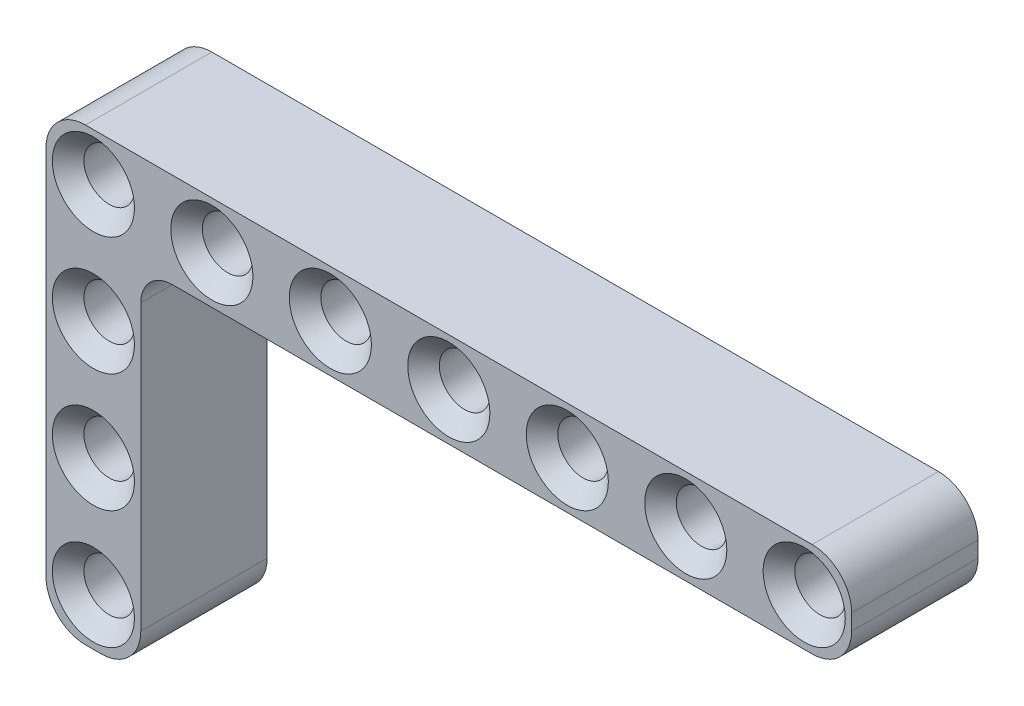
SolidWorks part; units mm, degrees
ref_plane "Front Plane" through (0, 0, 0) normal (0, 0, 1) x (1, 0, 0)
ref_plane "Top Plane" through (0, 0, 0) normal (0, 1, 0) x (1, 0, 0)
ref_plane "Right Plane" through (0, 0, 0) normal (1, 0, 0) x (0, 0, -1)
sketch "Sketch1" plane through (0, 0, 0) normal (0, 0, 1) x (1, 0, 0)
  line L1 (-0.5, 3) -> (45.5, 3)
  line L2 (-3, 0.5) -> (-3, -0.5)
  line L3 (-0.5, -3) -> (45.5, -3)
  line L4 (48, 0.5) -> (48, -0.5)
  circle A0 centre (0, 0) radius 1.6
  arc A1 (45.5, -3) -> (48, -0.5) centre (45.5, -0.5) ccw
  arc A2 (45.5, 3) -> (48, 0.5) centre (45.5, 0.5) cw
  arc A3 (-3, -0.5) -> (-0.5, -3) centre (-0.5, -0.5) ccw
  arc A4 (-0.5, 3) -> (-3, 0.5) centre (-0.5, 0.5) ccw
  circle A5 centre (7.5, 0) radius 1.6
  circle A6 centre (15, 0) radius 1.6
  circle A7 centre (22.5, 0) radius 1.6
  circle A8 centre (30, 0) radius 1.6
  circle A9 centre (37.5, 0) radius 1.6
  circle A10 centre (45, 0) radius 1.6
  point P8 (-3, 0)
  point P14 (-3, -3)
  point P17 (-3, 3)
  dimension "D1" = 3.2
  dimension "D4" = 2.5
  dimension "D2" = 6
  dimension "D3" = 3
  dimension "D6" = 7.5
  dimension "D5" = 7
extrude "Boss-Extrude1" add sketch "Sketch1" along normal blind 8
chamfer "Chamfer1" distance 1 angle 45 10 edges at (31.6, 0, 0) (31.6, 0, 8) (24.1, 0, 0) (24.1, 0, 8) (16.6, 0, 0) (16.6, 0, 8) (9.1, 0, 0) (9.1, 0, 8) (1.6, 0, 0) (1.6, 0, 8)
sketch "Sketch2" plane through (0, 0, 8) normal (0, 0, 1) x (1, 0, 0)
  line L0 (-3, 0) -> (-3, -23)
  line L1 (-0.5, -25.5) -> (0.5, -25.5)
  line L2 (3, -23) -> (3, -3)
  line L3 (-3, 0.5) -> (-3, -0.5) construction
  line L4 (-0.5, -3) -> (45.5, -3) construction
  circle A1 centre (0, -7.5) radius 1.6
  arc A4 (-3, -23) -> (-0.5, -25.5) centre (-0.5, -23) ccw
  arc A5 (0.5, -25.5) -> (3, -23) centre (0.5, -23) ccw
  circle A6 centre (0, -15) radius 1.6
  circle A7 centre (0, -22.5) radius 1.6
  point P18 (-3, -25.5)
  point P21 (3, -25.5)
  dimension "D3" = 3.2
  dimension "D8" = 2.5
  dimension "D1" = 6
  dimension "D2" = 90
  dimension "D4" = 3
  dimension "D5" = 7.5
  dimension "D7" = 3
  dimension "D6" = 3
extrude "Boss-Extrude3" add sketch "Sketch2" against normal blind 8
fillet "Fillet1" radius 2 1 edges at (3, -3, 4)
chamfer "Chamfer3" distance 1 angle 45 4 edges at (46.6, 0, 0) (46.6, 0, 8) (39.1, 0, 0) (39.1, 0, 8)
chamfer "Chamfer5" distance 1 angle 45 6 edges at (1.6, -7.5, 8) (1.6, -7.5, 0) (1.6, -15, 8) (1.6, -15, 0) (1.6, -22.5, 8) (1.6, -22.5, 0)
